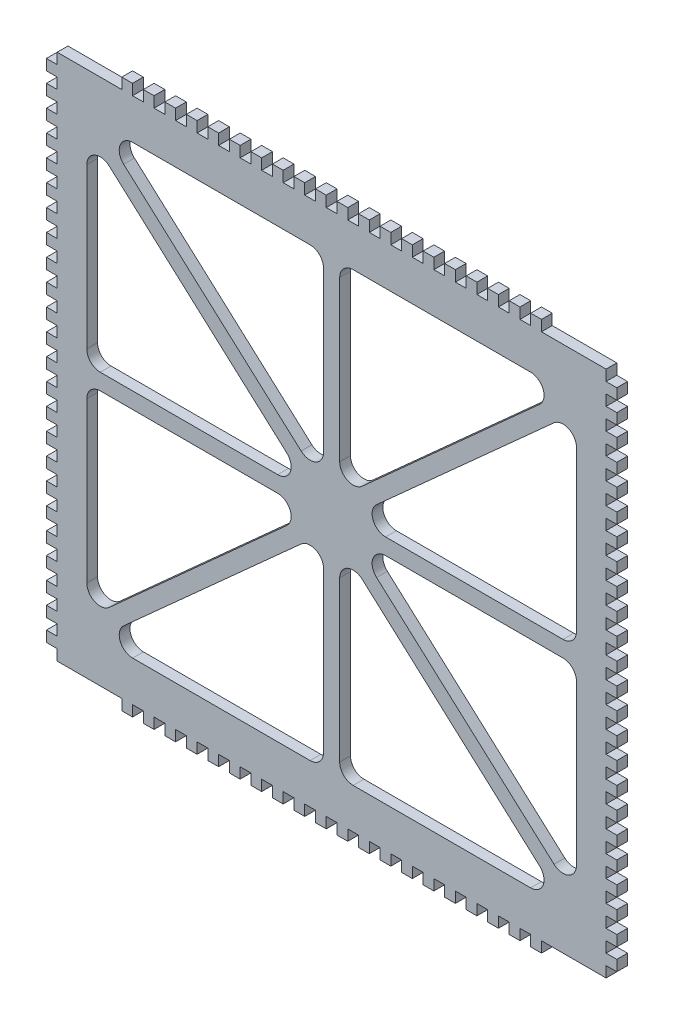
SolidWorks part; units mm, degrees
material "Cedar"
ref_plane "Front Plane" through (0, 0, 0) normal (0, 0, 1) x (1, 0, 0)
ref_plane "Top Plane" through (0, 0, 0) normal (0, 1, 0) x (1, 0, 0)
ref_plane "Right Plane" through (0, 0, 0) normal (1, 0, 0) x (0, 0, -1)
sketch "Sketch1" plane through (0, 0, 0) normal (0, 0, 1) x (1, 0, 0)
  line L0 (0, 0) -> (0, 50) construction
  line L1 (0, 0) -> (-64, 0) construction
  line L2 (-106, -98) -> (-106, 98)
  line L3 (-106, 98) -> (106, 98)
  line L5 (-73.9515, 83) -> (-8, 83)
  line L6 (5.0062, -5.2305) -> (7.0123, -3) construction
  line L7 (106, -98) -> (106, 98)
  line L8 (-106, -98) -> (106, -98)
  line L9 (3, -7.4611) -> (5.0062, -5.2305) construction
  line L10 (-82.6564, 71.0346) -> (-16.7049, 11.7176)
  line L11 (-20.0485, 3) -> (-86, 3)
  line L12 (8, 83) -> (73.9515, 83)
  line L13 (-77.2951, 74.2824) -> (-11.3436, 14.9654)
  line L14 (-3, 18.6829) -> (-3, 78)
  line L15 (66.3108, 56.3334) -> (62.2985, 60.7945) construction
  line L16 (3, 78) -> (3, 18.6829)
  line L17 (11.3436, 14.9654) -> (77.2951, 74.2824)
  line L18 (64.3047, 58.5639) -> (93.3405, 84.6789) construction
  line L19 (82.6564, 71.0346) -> (16.7049, 11.7176)
  line L20 (20.0485, 3) -> (86, 3)
  line L21 (86.9877, 83) -> (88.9938, 80.7695) construction
  line L22 (88.9938, 80.7695) -> (91, 78.5389) construction
  line L23 (-78.5236, 75.3874) -> (-82.5359, 70.9263) construction
  line L24 (-82.5359, 70.9263) -> (-80.5298, 73.1568) construction
  line L25 (-80.5298, 73.1568) -> (-93.4041, 84.7361) construction
  line L26 (-86.9877, 83) -> (-88.9938, 80.7695) construction
  line L27 (-88.9938, 80.7695) -> (-91, 78.5389) construction
  line L28 (9.2386, -9.0372) -> (4.4453, -4.7261) construction
  line L29 (7.2324, -11.2678) -> (11.2448, -6.8067) construction
  line L30 (-5.0062, -5.2305) -> (-7.0123, -3) construction
  line L31 (-3, -7.4611) -> (-5.0062, -5.2305) construction
  line L32 (-10.2311, -9.9299) -> (-3.5713, -3.9401) construction
  line L33 (-12.2373, -7.6994) -> (-10.2311, -9.9299) construction
  line L34 (-8.225, -12.1604) -> (-12.2373, -7.6994) construction
  line L35 (-88.9938, -80.7695) -> (-91, -78.5389) construction
  line L36 (-86.9877, -83) -> (-88.9938, -80.7695) construction
  line L37 (-82.5359, -70.9263) -> (-80.5298, -73.1568) construction
  line L38 (-78.5236, -75.3874) -> (-82.5359, -70.9263) construction
  line L39 (88.9938, -80.7695) -> (91, -78.5389) construction
  line L40 (86.9877, -83) -> (88.9938, -80.7695) construction
  line L41 (66.3108, -56.3334) -> (62.2985, -60.7945) construction
  line L42 (-91, -8) -> (-91, -67.3171)
  line L43 (91, -8) -> (91, -67.3171)
  line L44 (20.0485, -3) -> (86, -3)
  line L45 (82.6564, -71.0346) -> (16.7049, -11.7176)
  line L46 (91, 8) -> (91, 67.3171)
  line L47 (-91, 8) -> (-91, 67.3171)
  line L48 (-8.225, 12.1604) -> (-12.2373, 7.6994) construction
  line L49 (-12.2373, 7.6994) -> (-10.2311, 9.9299) construction
  line L50 (-10.2311, 9.9299) -> (-3.5713, 3.9401) construction
  line L51 (-3, 7.4611) -> (-5.0062, 5.2305) construction
  line L52 (-5.0062, 5.2305) -> (-7.0123, 3) construction
  line L53 (7.2324, 11.2678) -> (11.2448, 6.8067) construction
  line L54 (9.2386, 9.0372) -> (4.4453, 4.7261) construction
  line L55 (3, 7.4611) -> (5.0062, 5.2305) construction
  line L56 (5.0062, 5.2305) -> (7.0123, 3) construction
  line L57 (11.3436, -14.9654) -> (77.2951, -74.2824)
  line L58 (3, -78) -> (3, -18.6829)
  line L59 (-3, -18.6829) -> (-3, -78)
  line L60 (-77.2951, -74.2824) -> (-11.3436, -14.9654)
  line L61 (8, -83) -> (73.9515, -83)
  line L62 (-20.0485, -3) -> (-86, -3)
  line L63 (-82.6564, -71.0346) -> (-16.7049, -11.7176)
  line L64 (-73.9515, -83) -> (-8, -83)
  arc A0 (82.6564, 71.0346) -> (91, 67.3171) centre (86, 67.3171) cw
  arc A1 (86, 3) -> (91, 8) centre (86, 8) ccw
  arc A2 (16.7049, 11.7176) -> (20.0485, 3) centre (20.0485, 8) ccw
  arc A3 (3, 18.6829) -> (11.3436, 14.9654) centre (8, 18.6829) ccw
  arc A4 (77.2951, 74.2824) -> (73.9515, 83) centre (73.9515, 78) ccw
  arc A5 (3, 78) -> (8, 83) centre (8, 78) cw
  arc A6 (-77.2951, 74.2824) -> (-73.9515, 83) centre (-73.9515, 78) cw
  arc A7 (-11.3436, 14.9654) -> (-3, 18.6829) centre (-8, 18.6829) ccw
  arc A8 (-3, 78) -> (-8, 83) centre (-8, 78) ccw
  arc A9 (-16.7049, 11.7176) -> (-20.0485, 3) centre (-20.0485, 8) cw
  arc A10 (-91, 8) -> (-86, 3) centre (-86, 8) ccw
  arc A11 (-82.6564, 71.0346) -> (-91, 67.3171) centre (-86, 67.3171) ccw
  arc A12 (-82.6564, -71.0346) -> (-91, -67.3171) centre (-86, -67.3171) cw
  arc A13 (-91, -8) -> (-86, -3) centre (-86, -8) cw
  arc A14 (-16.7049, -11.7176) -> (-20.0485, -3) centre (-20.0485, -8) ccw
  arc A15 (-3, -78) -> (-8, -83) centre (-8, -78) cw
  arc A16 (-11.3436, -14.9654) -> (-3, -18.6829) centre (-8, -18.6829) cw
  arc A17 (-77.2951, -74.2824) -> (-73.9515, -83) centre (-73.9515, -78) ccw
  arc A18 (3, -78) -> (8, -83) centre (8, -78) ccw
  arc A19 (77.2951, -74.2824) -> (73.9515, -83) centre (73.9515, -78) cw
  arc A20 (3, -18.6829) -> (11.3436, -14.9654) centre (8, -18.6829) cw
  arc A21 (16.7049, -11.7176) -> (20.0485, -3) centre (20.0485, -8) cw
  arc A22 (86, -3) -> (91, -8) centre (86, -8) cw
  arc A23 (82.6564, -71.0346) -> (91, -67.3171) centre (86, -67.3171) ccw
  point P19 (0, 83)
  point P21 (0, 98)
  point P27 (-64, 0)
  point P28 (64, 0)
  point P29 (87, 0)
  point P34 (-87, 0)
  point P76 (91, 3)
  point P88 (3, 83)
  point P97 (-3, 83)
  point P103 (-91, 3)
  point P144 (-91, -3)
  point P145 (-3, -83)
  point P146 (3, -83)
  point P147 (91, -3)
  point P148 (0, -83)
  dimension "D3" = 15
  dimension "D8" = 98
  dimension "D7" = 6
  dimension "D9" = 6
  dimension "D10" = 3
  dimension "D11" = 98
  dimension "D12" = 5
  dimension "D2" = 212
  dimension "D4" = 15
  dimension "D5" = 3
  dimension "D6" = 3
  dimension "D13" = 15
extrude "Boss-Extrude1" add sketch "Sketch1" along normal blind 4
sketch "Sketch2" plane through (0, 0, 4) normal (0, 0, 1) x (1, 0, 0)
  line L0 (0, 0) -> (-89.2695, 0) construction
  line L1 (0, 0) -> (0, 71.1996) construction
  line L2 (-106, -50) -> (-102, -50)
  line L5 (-106, 86) -> (-102, 86)
  line L6 (-106, 86) -> (-106, 90)
  line L7 (-106, 90) -> (-102, 90)
  line L8 (-102, 86) -> (-102, 90)
  line L9 (-106, 78) -> (-102, 78)
  line L10 (-106, 78) -> (-106, 82)
  line L11 (-106, 82) -> (-102, 82)
  line L12 (-102, 78) -> (-102, 82)
  line L13 (-106, 70) -> (-102, 70)
  line L14 (-106, 70) -> (-106, 74)
  line L15 (-106, 74) -> (-102, 74)
  line L16 (-102, 70) -> (-102, 74)
  line L17 (-106, 62) -> (-102, 62)
  line L18 (-106, 62) -> (-106, 66)
  line L19 (-106, 66) -> (-102, 66)
  line L20 (-102, 62) -> (-102, 66)
  line L21 (-106, 54) -> (-102, 54)
  line L22 (-106, 54) -> (-106, 58)
  line L23 (-106, 58) -> (-102, 58)
  line L24 (-102, 54) -> (-102, 58)
  line L25 (-106, 46) -> (-102, 46)
  line L26 (-106, 46) -> (-106, 50)
  line L27 (-106, 50) -> (-102, 50)
  line L28 (-102, 46) -> (-102, 50)
  line L29 (-106, 38) -> (-102, 38)
  line L30 (-106, 38) -> (-106, 42)
  line L31 (-106, 42) -> (-102, 42)
  line L32 (-102, 38) -> (-102, 42)
  line L33 (-106, 30) -> (-102, 30)
  line L34 (-106, 30) -> (-106, 34)
  line L35 (-106, 34) -> (-102, 34)
  line L36 (-102, 30) -> (-102, 34)
  line L37 (-106, 22) -> (-102, 22)
  line L38 (-106, 22) -> (-106, 26)
  line L39 (-106, 26) -> (-102, 26)
  line L40 (-102, 22) -> (-102, 26)
  line L41 (-106, 14) -> (-102, 14)
  line L42 (-106, 14) -> (-106, 18)
  line L43 (-106, 18) -> (-102, 18)
  line L44 (-102, 14) -> (-102, 18)
  line L45 (-106, 6) -> (-102, 6)
  line L46 (-106, 6) -> (-106, 10)
  line L47 (-106, 10) -> (-102, 10)
  line L48 (-102, 6) -> (-102, 10)
  line L49 (-106, -2) -> (-102, -2)
  line L50 (-106, -2) -> (-106, 2)
  line L51 (-106, 2) -> (-102, 2)
  line L52 (-102, -2) -> (-102, 2)
  line L53 (-106, -10) -> (-102, -10)
  line L54 (-106, -10) -> (-106, -6)
  line L55 (-106, -6) -> (-102, -6)
  line L56 (-102, -10) -> (-102, -6)
  line L57 (-106, -18) -> (-102, -18)
  line L58 (-106, -18) -> (-106, -14)
  line L59 (-106, -14) -> (-102, -14)
  line L60 (-102, -18) -> (-102, -14)
  line L61 (-106, -26) -> (-102, -26)
  line L62 (-106, -26) -> (-106, -22)
  line L63 (-106, -22) -> (-102, -22)
  line L64 (-102, -26) -> (-102, -22)
  line L65 (-106, -34) -> (-102, -34)
  line L66 (-106, -34) -> (-106, -30)
  line L67 (-106, -30) -> (-102, -30)
  line L68 (-102, -34) -> (-102, -30)
  line L69 (-106, -42) -> (-102, -42)
  line L70 (-106, -42) -> (-106, -38)
  line L71 (-106, -38) -> (-102, -38)
  line L72 (-102, -42) -> (-102, -38)
  line L73 (102, -98) -> (102, -94)
  line L74 (106, -94) -> (102, -94)
  line L75 (106, -98) -> (106, -94)
  line L76 (106, -98) -> (102, -98)
  line L77 (102, -90) -> (102, -86)
  line L78 (106, -86) -> (102, -86)
  line L79 (106, -90) -> (106, -86)
  line L80 (106, -90) -> (102, -90)
  line L81 (102, -82) -> (102, -78)
  line L82 (106, -78) -> (102, -78)
  line L83 (106, -82) -> (106, -78)
  line L84 (106, -82) -> (102, -82)
  line L85 (102, -74) -> (102, -70)
  line L86 (106, -70) -> (102, -70)
  line L87 (106, -74) -> (106, -70)
  line L88 (106, -74) -> (102, -74)
  line L89 (102, -66) -> (102, -62)
  line L90 (106, -62) -> (102, -62)
  line L91 (106, -66) -> (106, -62)
  line L92 (106, -66) -> (102, -66)
  line L93 (102, -58) -> (102, -54)
  line L94 (106, -54) -> (102, -54)
  line L95 (106, -58) -> (106, -54)
  line L96 (106, -58) -> (102, -58)
  line L97 (102, -50) -> (102, -46)
  line L98 (106, -46) -> (102, -46)
  line L99 (106, -50) -> (106, -46)
  line L100 (102, 94) -> (102, 98)
  line L101 (106, 98) -> (102, 98)
  line L102 (106, 94) -> (106, 98)
  line L103 (-106, 94) -> (-102, 94)
  line L104 (-106, 94) -> (-106, 98)
  line L105 (-106, 98) -> (-102, 98)
  line L106 (-102, 94) -> (-102, 98)
  line L107 (106, 94) -> (102, 94)
  line L108 (102, -42) -> (102, -38)
  line L109 (106, -38) -> (102, -38)
  line L110 (106, -42) -> (106, -38)
  line L111 (106, -42) -> (102, -42)
  line L112 (102, -34) -> (102, -30)
  line L113 (106, -30) -> (102, -30)
  line L114 (106, -34) -> (106, -30)
  line L115 (106, -34) -> (102, -34)
  line L116 (102, -26) -> (102, -22)
  line L117 (106, -22) -> (102, -22)
  line L118 (106, -26) -> (106, -22)
  line L119 (106, -26) -> (102, -26)
  line L120 (102, -18) -> (102, -14)
  line L121 (106, -14) -> (102, -14)
  line L122 (106, -18) -> (106, -14)
  line L123 (106, -18) -> (102, -18)
  line L124 (102, -10) -> (102, -6)
  line L125 (106, -6) -> (102, -6)
  line L126 (106, -10) -> (106, -6)
  line L127 (106, -10) -> (102, -10)
  line L128 (102, -2) -> (102, 2)
  line L129 (106, 2) -> (102, 2)
  line L130 (106, -2) -> (106, 2)
  line L131 (-106, -50) -> (-106, -46)
  line L132 (106, -2) -> (102, -2)
  line L133 (102, 6) -> (102, 10)
  line L134 (106, 10) -> (102, 10)
  line L135 (106, 6) -> (106, 10)
  line L136 (106, 6) -> (102, 6)
  line L137 (102, 14) -> (102, 18)
  line L138 (106, 18) -> (102, 18)
  line L139 (106, 14) -> (106, 18)
  line L140 (106, 14) -> (102, 14)
  line L141 (102, 22) -> (102, 26)
  line L142 (106, 26) -> (102, 26)
  line L143 (106, 22) -> (106, 26)
  line L144 (106, 22) -> (102, 22)
  line L145 (102, 30) -> (102, 34)
  line L146 (106, 34) -> (102, 34)
  line L147 (106, 30) -> (106, 34)
  line L148 (106, 30) -> (102, 30)
  line L149 (102, 38) -> (102, 42)
  line L150 (-106, -46) -> (-102, -46)
  line L151 (-102, -50) -> (-102, -46)
  line L152 (-106, -58) -> (-102, -58)
  line L153 (-106, -58) -> (-106, -54)
  line L154 (-106, -54) -> (-102, -54)
  line L155 (-102, -58) -> (-102, -54)
  line L156 (106, 42) -> (102, 42)
  line L157 (106, 38) -> (106, 42)
  line L158 (106, 38) -> (102, 38)
  line L159 (102, 46) -> (102, 50)
  line L160 (106, 50) -> (102, 50)
  line L161 (106, 46) -> (106, 50)
  line L162 (106, 46) -> (102, 46)
  line L163 (102, 54) -> (102, 58)
  line L165 (-106, -98) -> (-106, 98) construction
  line L166 (-106, 98) -> (106, 98) construction
  line L167 (-106, -66) -> (-102, -66)
  line L168 (-106, -66) -> (-106, -62)
  line L169 (-106, -62) -> (-102, -62)
  line L170 (-102, -66) -> (-102, -62)
  line L171 (-106, -74) -> (-102, -74)
  line L172 (-106, -74) -> (-106, -70)
  line L173 (-106, -70) -> (-102, -70)
  line L174 (-102, -74) -> (-102, -70)
  line L175 (-106, -82) -> (-102, -82)
  line L176 (-106, -82) -> (-106, -78)
  line L177 (-106, -78) -> (-102, -78)
  line L178 (-102, -82) -> (-102, -78)
  line L179 (-106, -90) -> (-102, -90)
  line L180 (-106, -90) -> (-106, -86)
  line L181 (-106, -86) -> (-102, -86)
  line L182 (-102, -90) -> (-102, -86)
  line L183 (-106, -98) -> (-102, -98)
  line L184 (-106, -98) -> (-106, -94)
  line L185 (-106, -94) -> (-102, -94)
  line L186 (-102, -98) -> (-102, -94)
  line L187 (106, 58) -> (102, 58)
  line L188 (106, 54) -> (106, 58)
  line L189 (106, 54) -> (102, 54)
  line L190 (102, 62) -> (102, 66)
  line L191 (106, 66) -> (102, 66)
  line L192 (106, 62) -> (106, 66)
  line L193 (106, 62) -> (102, 62)
  line L194 (102, 70) -> (102, 74)
  line L195 (106, 74) -> (102, 74)
  line L196 (106, 70) -> (106, 74)
  line L197 (106, 70) -> (102, 70)
  line L198 (102, 78) -> (102, 82)
  line L199 (106, 82) -> (102, 82)
  line L200 (106, 78) -> (106, 82)
  line L201 (106, 78) -> (102, 78)
  line L202 (102, 86) -> (102, 90)
  line L203 (106, 90) -> (102, 90)
  line L204 (106, 86) -> (106, 90)
  line L205 (106, 86) -> (102, 86)
  line L206 (106, -50) -> (102, -50)
  dimension "D2" = 4
  dimension "D3" = 4
  dimension "D4" = 25
extrude "Cut-Extrude1" cut sketch "Sketch2" against normal blind 4
sketch "Sketch4" plane through (0, 0, 0) normal (0, 0, -1) x (-1, 0, 0)
  line L0 (0, 98) -> (0, 81.4646) construction
  line L1 (106, 98) -> (-106, 98) construction
  line L2 (-87, 0) -> (-48.0992, 0) construction
  line L3 (-10, 98) -> (-14, 98)
  line L4 (-2, 98) -> (-6, 98)
  line L5 (-2, 98) -> (-2, 102)
  line L6 (-2, 102) -> (-6, 102)
  line L7 (-6, 98) -> (-6, 102)
  line L8 (-10, 98) -> (-10, 102)
  line L9 (-10, 102) -> (-14, 102)
  line L10 (-14, 98) -> (-14, 102)
  line L11 (-18, 98) -> (-22, 98)
  line L12 (-18, 98) -> (-18, 102)
  line L13 (-18, 102) -> (-22, 102)
  line L14 (-22, 98) -> (-22, 102)
  line L15 (-26, 98) -> (-30, 98)
  line L16 (-26, 98) -> (-26, 102)
  line L17 (-26, 102) -> (-30, 102)
  line L18 (-30, 98) -> (-30, 102)
  line L19 (-34, 98) -> (-38, 98)
  line L20 (-34, 98) -> (-34, 102)
  line L21 (-34, 102) -> (-38, 102)
  line L22 (-38, 98) -> (-38, 102)
  line L23 (-42, 98) -> (-46, 98)
  line L24 (-42, 98) -> (-42, 102)
  line L25 (-42, 102) -> (-46, 102)
  line L26 (-46, 98) -> (-46, 102)
  line L27 (-50, 98) -> (-54, 98)
  line L28 (-50, 98) -> (-50, 102)
  line L29 (-50, 102) -> (-54, 102)
  line L30 (-54, 98) -> (-54, 102)
  line L31 (-58, 98) -> (-62, 98)
  line L32 (-58, 98) -> (-58, 102)
  line L33 (-58, 102) -> (-62, 102)
  line L34 (-62, 98) -> (-62, 102)
  line L35 (-66, 98) -> (-70, 98)
  line L36 (-66, 98) -> (-66, 102)
  line L37 (-66, 102) -> (-70, 102)
  line L38 (-70, 98) -> (-70, 102)
  line L39 (-74, 98) -> (-78, 98)
  line L40 (-74, 98) -> (-74, 102)
  line L41 (-74, 102) -> (-78, 102)
  line L42 (-78, 98) -> (-78, 102)
  line L43 (78, 98) -> (78, 102)
  line L44 (74, 102) -> (78, 102)
  line L45 (74, 98) -> (74, 102)
  line L46 (74, 98) -> (78, 98)
  line L47 (70, 98) -> (70, 102)
  line L48 (66, 102) -> (70, 102)
  line L49 (66, 98) -> (66, 102)
  line L50 (66, 98) -> (70, 98)
  line L51 (62, 98) -> (62, 102)
  line L52 (58, 102) -> (62, 102)
  line L53 (58, 98) -> (58, 102)
  line L54 (58, 98) -> (62, 98)
  line L55 (54, 98) -> (54, 102)
  line L56 (50, 102) -> (54, 102)
  line L57 (50, 98) -> (50, 102)
  line L58 (50, 98) -> (54, 98)
  line L59 (46, 98) -> (46, 102)
  line L60 (42, 102) -> (46, 102)
  line L61 (42, 98) -> (42, 102)
  line L62 (42, 98) -> (46, 98)
  line L63 (38, 98) -> (38, 102)
  line L64 (34, 102) -> (38, 102)
  line L65 (34, 98) -> (34, 102)
  line L66 (34, 98) -> (38, 98)
  line L67 (30, 98) -> (30, 102)
  line L68 (26, 102) -> (30, 102)
  line L69 (26, 98) -> (26, 102)
  line L70 (26, 98) -> (30, 98)
  line L71 (22, 98) -> (22, 102)
  line L72 (18, 102) -> (22, 102)
  line L73 (18, 98) -> (18, 102)
  line L74 (18, 98) -> (22, 98)
  line L75 (14, 98) -> (14, 102)
  line L76 (10, 102) -> (14, 102)
  line L77 (10, 98) -> (10, 102)
  line L78 (6, 98) -> (6, 102)
  line L79 (2, 102) -> (6, 102)
  line L80 (2, 98) -> (2, 102)
  line L81 (2, 98) -> (6, 98)
  line L82 (10, 98) -> (14, 98)
  line L83 (10, -98) -> (14, -98)
  line L84 (2, -98) -> (6, -98)
  line L85 (2, -98) -> (2, -102)
  line L86 (2, -102) -> (6, -102)
  line L87 (6, -98) -> (6, -102)
  line L88 (10, -98) -> (10, -102)
  line L89 (10, -102) -> (14, -102)
  line L90 (14, -98) -> (14, -102)
  line L91 (18, -98) -> (22, -98)
  line L92 (18, -98) -> (18, -102)
  line L93 (18, -102) -> (22, -102)
  line L94 (22, -98) -> (22, -102)
  line L95 (26, -98) -> (30, -98)
  line L96 (26, -98) -> (26, -102)
  line L97 (26, -102) -> (30, -102)
  line L98 (30, -98) -> (30, -102)
  line L99 (34, -98) -> (38, -98)
  line L100 (34, -98) -> (34, -102)
  line L101 (34, -102) -> (38, -102)
  line L102 (38, -98) -> (38, -102)
  line L103 (42, -98) -> (46, -98)
  line L104 (42, -98) -> (42, -102)
  line L105 (42, -102) -> (46, -102)
  line L106 (46, -98) -> (46, -102)
  line L107 (50, -98) -> (54, -98)
  line L108 (50, -98) -> (50, -102)
  line L109 (50, -102) -> (54, -102)
  line L110 (54, -98) -> (54, -102)
  line L111 (58, -98) -> (62, -98)
  line L112 (58, -98) -> (58, -102)
  line L113 (58, -102) -> (62, -102)
  line L114 (62, -98) -> (62, -102)
  line L115 (66, -98) -> (70, -98)
  line L116 (66, -98) -> (66, -102)
  line L117 (66, -102) -> (70, -102)
  line L118 (70, -98) -> (70, -102)
  line L119 (74, -98) -> (78, -98)
  line L120 (74, -98) -> (74, -102)
  line L121 (74, -102) -> (78, -102)
  line L122 (78, -98) -> (78, -102)
  line L123 (-78, -98) -> (-78, -102)
  line L124 (-74, -102) -> (-78, -102)
  line L125 (-74, -98) -> (-74, -102)
  line L126 (-74, -98) -> (-78, -98)
  line L127 (-70, -98) -> (-70, -102)
  line L128 (-66, -102) -> (-70, -102)
  line L129 (-66, -98) -> (-66, -102)
  line L130 (-66, -98) -> (-70, -98)
  line L131 (-62, -98) -> (-62, -102)
  line L132 (-58, -102) -> (-62, -102)
  line L133 (-58, -98) -> (-58, -102)
  line L134 (-58, -98) -> (-62, -98)
  line L135 (-54, -98) -> (-54, -102)
  line L136 (-50, -102) -> (-54, -102)
  line L137 (-50, -98) -> (-50, -102)
  line L138 (-50, -98) -> (-54, -98)
  line L139 (-46, -98) -> (-46, -102)
  line L140 (-42, -102) -> (-46, -102)
  line L141 (-42, -98) -> (-42, -102)
  line L142 (-42, -98) -> (-46, -98)
  line L143 (-38, -98) -> (-38, -102)
  line L144 (-34, -102) -> (-38, -102)
  line L145 (-34, -98) -> (-34, -102)
  line L146 (-34, -98) -> (-38, -98)
  line L147 (-30, -98) -> (-30, -102)
  line L148 (-26, -102) -> (-30, -102)
  line L149 (-26, -98) -> (-26, -102)
  line L150 (-26, -98) -> (-30, -98)
  line L151 (-22, -98) -> (-22, -102)
  line L152 (-18, -102) -> (-22, -102)
  line L153 (-18, -98) -> (-18, -102)
  line L154 (-18, -98) -> (-22, -98)
  line L155 (-14, -98) -> (-14, -102)
  line L156 (-10, -102) -> (-14, -102)
  line L157 (-10, -98) -> (-10, -102)
  line L158 (-6, -98) -> (-6, -102)
  line L159 (-2, -102) -> (-6, -102)
  line L160 (-2, -98) -> (-2, -102)
  line L161 (-2, -98) -> (-6, -98)
  line L162 (-10, -98) -> (-14, -98)
  dimension "D1" = 2
  dimension "D2" = 4
  dimension "D3" = 4
  dimension "D4" = 10
extrude "Boss-Extrude2" add sketch "Sketch4" against normal blind 4
